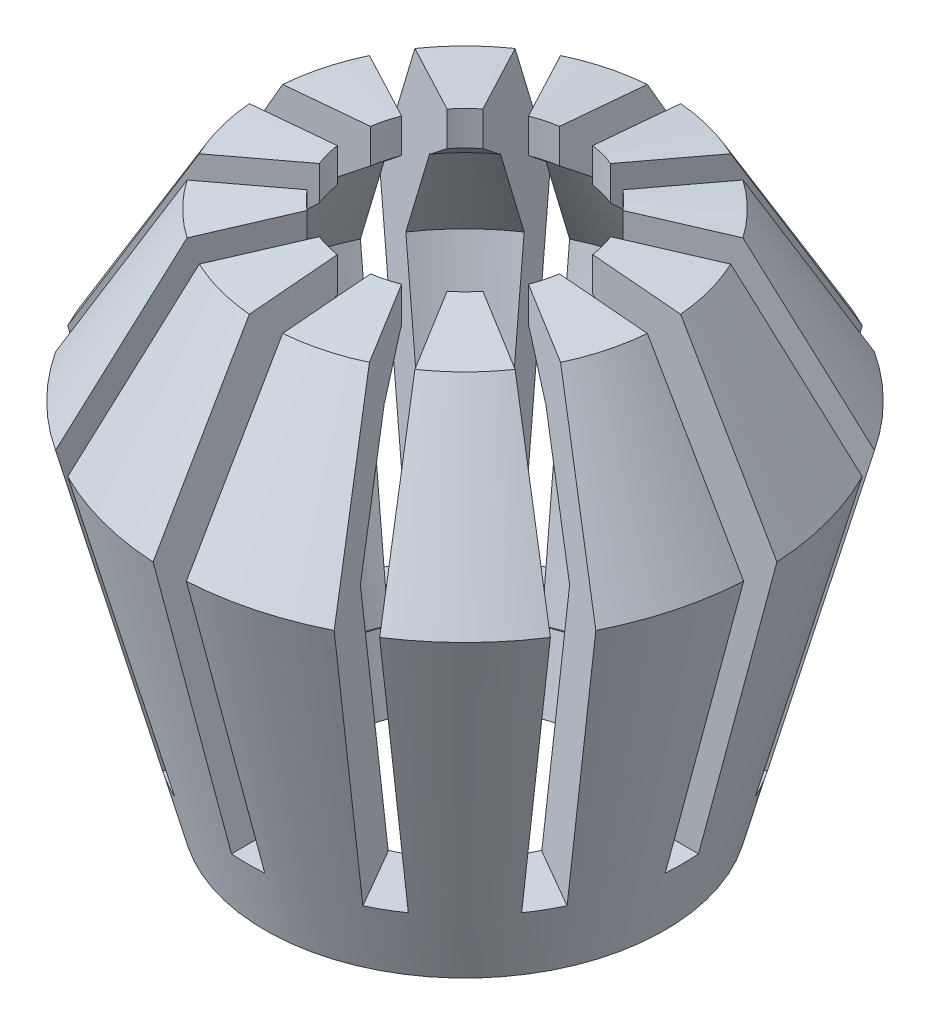
SolidWorks part; units mm, degrees
ref_plane "前视基准面" through (0, 0, 0) normal (0, 0, 1) x (1, 0, 0)
ref_plane "上视基准面" through (0, 0, 0) normal (0, 1, 0) x (1, 0, 0)
ref_plane "右视基准面" through (0, 0, 0) normal (1, 0, 0) x (0, 0, -1)
other "Configuration Table"
sketch "草图2" plane through (0, 0, 0) normal (0, 0, 1) x (1, 0, 0)
  line L0 (0, -736.8123) -> (0, 36073.3383) construction
  line L1 (0, 10) -> (-12, 10)
  line L2 (-12, 10) -> (-17.7735, 0)
  line L3 (-17.7735, 0) -> (-12, -21.547)
  line L4 (-12, -21.547) -> (0, -21.547)
  line L5 (-17.7735, 0) -> (0, 0) construction
  line L6 (0, 10) -> (0, -21.547)
  line L7 (-12, 10) -> (0, 11.0499)
  line L8 (0, 11.0499) -> (0, 10)
  dimension "D1" = 12
  dimension "D2" = 10
  dimension "D3" = 60
  dimension "D4" = 5
  dimension "D5" = 75
revolve "旋转1" add sketch "草图2" angle 360 about L0
sketch "草图7" plane through (0, 0, 0) normal (0, 0, 1) x (1, 0, 0)
  line L0 (0, 11.0499) -> (-12, 10)
  line L1 (12, 10) -> (0, 11.0499)
  line L2 (12, 10) -> (0, 11.0499)
  line L3 (0, 11.0499) -> (-12, 10)
  line L4 (-17.7735, 0) -> (-12, 10)
  line L5 (12, 10) -> (17.7735, 0)
  line L6 (12, 10) -> (17.7735, 0)
  line L7 (-17.7735, 0) -> (-12, 10)
  line L8 (17.7735, 0) -> (12, -21.547)
  line L9 (-12, -21.547) -> (-17.7735, 0)
  line L10 (-12, -21.547) -> (-17.7735, 0)
  line L11 (17.7735, 0) -> (12, -21.547)
  line L12 (12, -21.547) -> (-12, -21.547)
  line L13 (12, -21.547) -> (-12, -21.547)
  line L14 (9.577, 6.1967) -> (13.481, -0.5651)
  line L15 (13.481, -0.5651) -> (8.9307, -17.547)
  line L16 (8.9307, -17.547) -> (-8.9307, -17.547)
  line L17 (-8.9307, -17.547) -> (-13.481, -0.5651)
  line L18 (-13.481, -0.5651) -> (-9.577, 6.1967)
  line L19 (0, 7.0346) -> (-9.577, 6.1967)
  line L20 (9.577, 6.1967) -> (0, 7.0346)
  line L21 (0, -1000) -> (0, 49000) construction
  dimension "D1" = 4
revolve "切除-旋转2" cut sketch "草图7" angle 360 about L21
ref_plane "基准面1" through (0, 10, 0) normal (0, 1, 0) x (1, 0, 0)
sketch "草图6" plane through (0, 10, 0) normal (0, 1, 0) x (1, 0, 0)
  circle A0 centre (0, 0) radius 6.75
  dimension "D1" = 13.5
extrude "切除-拉伸3" cut sketch "草图6" against normal through all and the other way through all
sketch "草图8" plane through (0, 10, 0) normal (0, 1, 0) x (1, 0, 0)
  line L0 (9.7528, 14.8923) -> (-8.0207, -15.8923)
  line L1 (-1, 17.7735) -> (1, 17.7735)
  line L2 (-1, 17.7735) -> (-1, -17.7735)
  line L3 (-1, -17.7735) -> (1, -17.7735)
  line L4 (1, 17.7735) -> (1, -17.7735)
  line L5 (-1, 17.7735) -> (1, -17.7735) construction
  line L6 (-1, -17.7735) -> (1, 17.7735) construction
  line L7 (8.0207, 15.8923) -> (9.7528, 14.8923)
  line L8 (8.0207, 15.8923) -> (-9.7528, -14.8923)
  line L9 (-9.7528, -14.8923) -> (-8.0207, -15.8923)
  line L10 (15.8923, 8.0207) -> (-14.8923, -9.7528)
  line L11 (14.8923, 9.7528) -> (15.8923, 8.0207)
  line L12 (14.8923, 9.7528) -> (-15.8923, -8.0207)
  line L13 (-15.8923, -8.0207) -> (-14.8923, -9.7528)
  line L14 (17.7735, -1) -> (-17.7735, -1)
  line L15 (17.7735, 1) -> (17.7735, -1)
  line L16 (17.7735, 1) -> (-17.7735, 1)
  line L17 (-17.7735, 1) -> (-17.7735, -1)
  line L18 (14.8923, -9.7528) -> (-15.8923, 8.0207)
  line L19 (15.8923, -8.0207) -> (14.8923, -9.7528)
  line L20 (15.8923, -8.0207) -> (-14.8923, 9.7528)
  line L21 (-14.8923, 9.7528) -> (-15.8923, 8.0207)
  line L22 (8.0207, -15.8923) -> (-9.7528, 14.8923)
  line L23 (9.7528, -14.8923) -> (8.0207, -15.8923)
  line L24 (9.7528, -14.8923) -> (-8.0207, 15.8923)
  line L25 (-8.0207, 15.8923) -> (-9.7528, 14.8923)
  line L26 (0, 0) -> (1, -17.7735) construction
  line L27 (0, 0) -> (-8.0207, -15.8923) construction
  circle A0 centre (0, 0) radius 17.7735 construction
  point P0 (0, 0)
  point P8 (15.8125, 14.8205)
  point P9 (0, 0)
  dimension "D1" = 2
  dimension "D3" = 30
  dimension "D2" = 6
extrude "切除-拉伸4" cut sketch "草图8" against normal up to surface and the other way through all contours L24 L25 L22 L23 | L18 L21 L20 L19 | L14 L17 L16 L15 | L10 L13 L12 L11 | L8 L9 L0 L7 | L2 L3 L4 L1
sketch "草图10" plane through (0, 0, 0) normal (0, 0, 1) x (1, 0, 0)
  line L0 (6.6755, 6.444) -> (6.6755, 10.4593) construction
  line L1 (6.6755, 6.444) -> (6.6755, 10.4593)
  line L2 (9.5247, 6.1967) -> (6.6755, 8.4593)
  line L4 (0, -1000) -> (0, 49000) construction
  spline S0 degree 3 poles (899.9496, 2826.4821) (-7.3467, -2890.9557) (28.9143, 2903.9416) (-878.6462, -2816.72) knots -229.756768 -229.756768 -229.756768 -229.756768 228.896083 228.896083 228.896083 228.896083 only from (9.5247, 6.1967) to (6.6755, 6.444) construction
  spline S1 degree 3 poles (9.5247, 6.1967) (8.575, 6.2793) (7.6253, 6.3619) (6.6755, 6.444) knots 0 0 0 0 1 1 1 1
  dimension "D1" = 2
revolve "切除-旋转3" cut sketch "草图10" angle 360 about L4
sketch "草图11" plane through (0, 0, 0) normal (0, 0, 1) x (1, 0, 0)
  line L0 (12, -21.547) -> (6.75, -21.547)
  line L1 (-6.75, -21.547) -> (-12, -21.547)
  line L2 (8.8745, -17.547) -> (7.7959, -21.547)
  line L3 (7.7959, -21.547) -> (6.75, -21.547)
  line L4 (13.0718, -17.547) -> (6.75, -17.547)
  line L5 (-6.75, -17.547) -> (-13.0718, -17.547)
  line L6 (0, -1000) -> (0, 49000) construction
  line L7 (8.8745, -17.547) -> (6.75, -17.547)
  line L8 (6.75, -21.547) -> (6.75, -17.547)
  line L9 (-6.75, -17.547) -> (-6.75, -21.547)
  line L11 (6.75, -21.547) -> (6.75, -17.547)
  spline S0 degree 3 poles (2649.2357, 918.0362) (-2083.994, 1121.1286) (2121.2227, -1120.1461) (-2648.5535, -907.5737) knots -89.928943 -89.928943 -89.928943 -89.928943 89.665 89.665 89.665 89.665 only from (13.4438, -0.5651) to (8.8745, -17.547) construction
  spline S1 degree 3 poles (13.4438, -0.5651) (11.9227, -6.2263) (10.4007, -11.8872) (8.8745, -17.547) knots 0 0 0 0 1 1 1 1
revolve "切除-旋转4" cut sketch "草图11" angle 360 about L6
